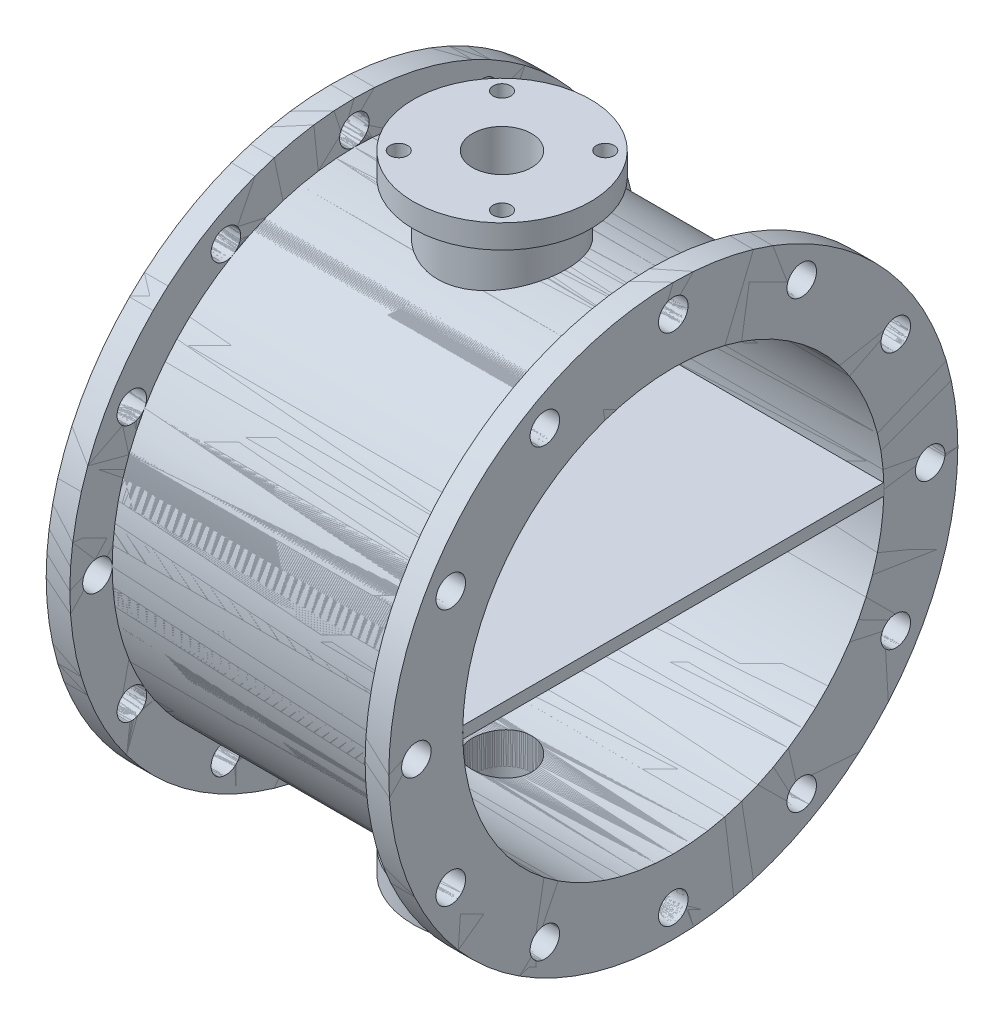
SolidWorks part; units mm, degrees
ref_plane "Front Plane" through (0, 0, 0) normal (0, 0, 1) x (1, 0, 0)
ref_plane "Top Plane" through (0, 0, 0) normal (0, 1, 0) x (1, 0, 0)
ref_plane "Right Plane" through (0, 0, 0) normal (1, 0, 0) x (0, 0, -1)
sketch "Sketch1" plane through (0, 0, 0) normal (1, 0, 0) x (0, 0, -1)
  circle A0 centre (0, 0) radius 2408.8383
  circle A1 centre (0, 0) radius 1782.5403
  circle A2 centre (0, 0) radius 2175 construction
  circle A3 centre (0, 2175) radius 125
  circle A4 centre (1087.5, 1883.6053) radius 125
  circle A5 centre (1883.6053, 1087.5) radius 125
  circle A6 centre (2175, 0) radius 125
  circle A7 centre (1883.6053, -1087.5) radius 125
  circle A8 centre (1087.5, -1883.6053) radius 125
  circle A9 centre (0, -2175) radius 125
  circle A10 centre (-1087.5, -1883.6053) radius 125
  circle A11 centre (-1883.6053, -1087.5) radius 125
  circle A12 centre (-2175, 0) radius 125
  circle A13 centre (-1883.6053, 1087.5) radius 125
  circle A14 centre (-1087.5, 1883.6053) radius 125
  point P31 (0, 0)
  dimension "D1" = 4350
  dimension "D2" = 12
extrude "Boss-Extrude1" add sketch "Sketch1" along normal blind 200
sketch "Sketch2" plane through (200, 0, 0) normal (1, 0, 0) x (0, 0, -1)
  circle A0 centre (0, 0) radius 1782.5403
  circle A1 centre (0, 0) radius 2050
extrude "Boss-Extrude3" add sketch "Sketch2" along normal blind 2500
ref_plane "Plane2" through (1450, 0, 0) normal (1, 0, 0) x (0, 0, -1)
mirror "Mirror2" about plane through (1450, 0, 0) normal (1, 0, 0) of "Boss-Extrude1"
sketch "Sketch3" plane through (0, 0, 0) normal (-1, 0, 0) x (0, 0, 1)
  line L1 (-1781.8389, 50) -> (1781.8389, 50)
  line L2 (-1781.8389, 50) -> (-1781.8389, -50)
  line L3 (-1781.8389, -50) -> (1781.8389, -50)
  line L4 (1781.8389, 50) -> (1781.8389, -50)
  line L5 (-1781.8389, 50) -> (1781.8389, -50) construction
  line L6 (-1781.8389, -50) -> (1781.8389, 50) construction
  circle A0 centre (0, 0) radius 1782.5403 construction
  point P0 (0, 0)
  dimension "D1" = 100
extrude "Boss-Extrude4" add sketch "Sketch3" against normal blind 2900 separate body
ref_plane "Plane3" through (0, 2650, 0) normal (0, 1, 0) x (1, 0, 0)
sketch "Sketch4" plane through (0, 2650, 0) normal (0, 1, 0) x (1, 0, 0)
  line L0 (1450, -2649.7221) -> (1450, 2649.7221) construction
  line L1 (1450, 0) -> (3344.1167, 0) construction
  line L2 (1450, 0) -> (3390.7436, 1940.7436) construction
  circle A0 centre (1450, 0) radius 750
  circle A1 centre (1450, 0) radius 625 construction
  circle A4 centre (1887.093, 437.093) radius 75
  circle A5 centre (1887.093, -437.093) radius 75
  circle A6 centre (1012.907, -437.093) radius 75
  circle A7 centre (1012.907, 437.093) radius 75
  point P21 (1450, 0)
  dimension "D1" = 1500
  dimension "D2" = 1250
  dimension "D4" = 4
  dimension "D3" = 45
extrude "Boss-Extrude15" add sketch "Sketch4" against normal blind 200 separate body contours A6 | A0 | A5 | A4 | A7
sketch "Sketch11" plane through (0, 2650, 0) normal (0, 1, 0) x (1, 0, 0)
  circle A0 centre (1450, 0) radius 543.1428
  circle A1 centre (1450, 0) radius 250
  dimension "D1" = 500
extrude "Boss-Extrude17" add sketch "Sketch11" against normal up to surface contours A1 | A0
sketch "Sketch12" plane through (0, 2650, 0) normal (0, 1, 0) x (1, 0, 0)
  line L0 (1450, -2649.7221) -> (1450, 2649.7221) construction
  circle A0 centre (1450, 0) radius 250
  dimension "D1" = 500
extrude "Cut-Extrude4" cut sketch "Sketch12" against normal blind 1310
mirror "Mirror14" about plane through (0, 0, 0) normal (0, 1, 0) of bodies 127
sketch "Sketch13" plane through (0, 2650, 0) normal (0, 1, 0) x (1, 0, 0)
  circle A0 centre (1450, 0) radius 250
extrude "Cut-Extrude5" cut sketch "Sketch13" against normal blind 1310
sketch "Sketch14" plane through (0, -2650, 0) normal (0, -1, 0) x (1, 0, 0)
  circle A0 centre (1450, 0) radius 250
extrude "Cut-Extrude6" cut sketch "Sketch14" against normal blind 1310
